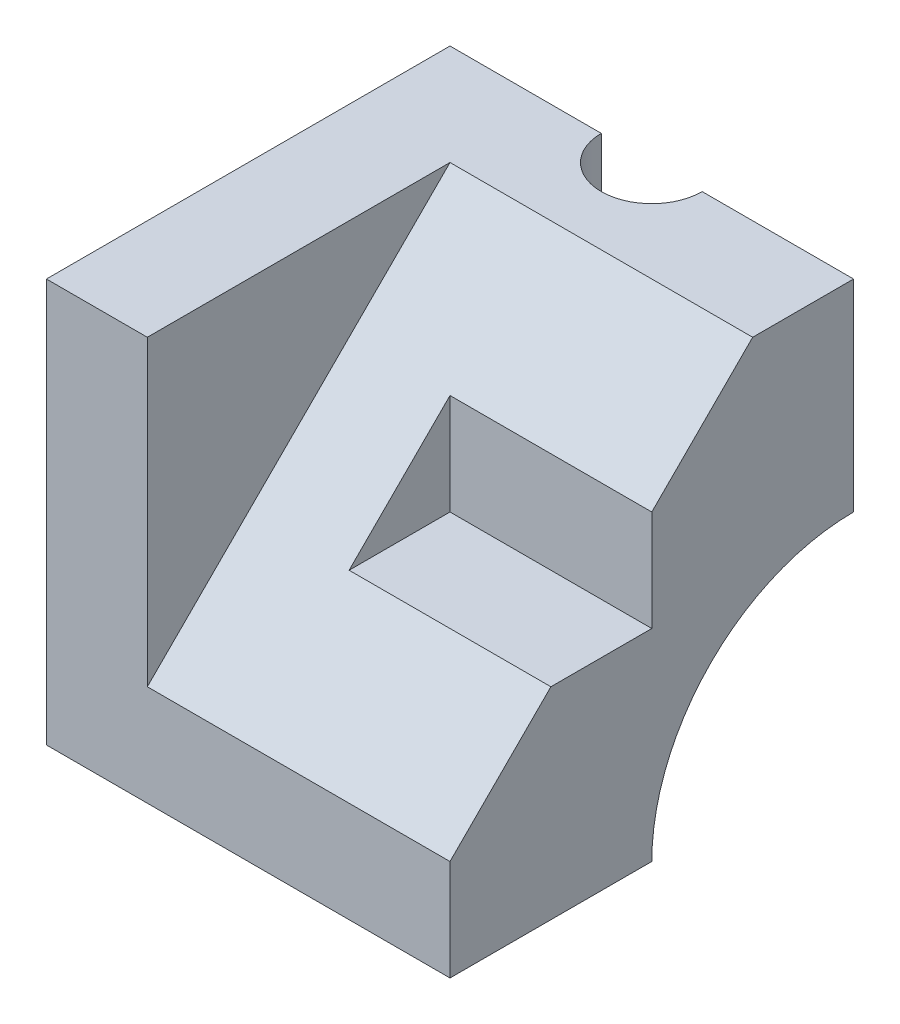
SolidWorks part; units mm, degrees
ref_plane "Front Plane" through (0, 0, 0) normal (0, 0, 1) x (1, 0, 0)
ref_plane "Top Plane" through (0, 0, 0) normal (0, 1, 0) x (1, 0, 0)
ref_plane "Right Plane" through (0, 0, 0) normal (1, 0, 0) x (0, 0, -1)
sketch "Sketch1" plane through (0, 0, 0) normal (0, 0, 1) x (1, 0, 0)
  line L0 (0, 0) -> (0, 80)
  line L1 (0, 80) -> (20, 80)
  line L2 (20, 80) -> (20, 0)
  line L3 (20, 0) -> (0, 0)
  dimension "D1" = 80
  dimension "D2" = 20
extrude "Boss-Extrude1" add sketch "Sketch1" along normal mid plane 80
sketch "Sketch2" plane through (0, 0, 0) normal (1, 0, 0) x (0, 0, -1)
  line L0 (40, 80) -> (20, 80)
  line L1 (-40, 80) -> (40, 80) construction
  line L2 (40, 0) -> (40, 80) construction
  line L3 (40, 80) -> (40, 40)
  line L4 (0, 0) -> (-40, 0)
  line L5 (-40, 0) -> (-40, 20)
  line L6 (-40, 0) -> (-40, 80) construction
  line L7 (-40, 20) -> (20, 80)
  arc A0 (0, 0) -> (40, 40) centre (40, 0) cw
  dimension "D1" = 20
  dimension "D2" = 20
extrude "Boss-Extrude2" add sketch "Sketch2" along normal blind 80
sketch "Sketch4" plane through (80, 0, 0) normal (1, 0, 0) x (0, 0, -1)
  line L2 (20, 80) -> (-40, 20) construction
  line L3 (0, 60) -> (0, 40)
  line L4 (0, 40) -> (-20, 40)
  line L5 (20, 80) -> (-40, 20) construction
  line L6 (-20, 40) -> (0, 60)
  dimension "D1" = 20
extrude "Cut-Extrude2" cut sketch "Sketch4" against normal blind 40
sketch "Sketch5" plane through (0, 0, 0) normal (0, 1, 0) x (1, 0, 0)
  line L1 (80, 40) -> (20, 40) construction
  line L3 (40, 40) -> (50, 40)
  line L4 (40, 40) -> (30, 40)
  arc A0 (30, 40) -> (50, 40) centre (40, 40) ccw
  dimension "D2" = 10
  dimension "D1" = 10
extrude "Cut-Extrude4" cut sketch "Sketch5" along normal through all
